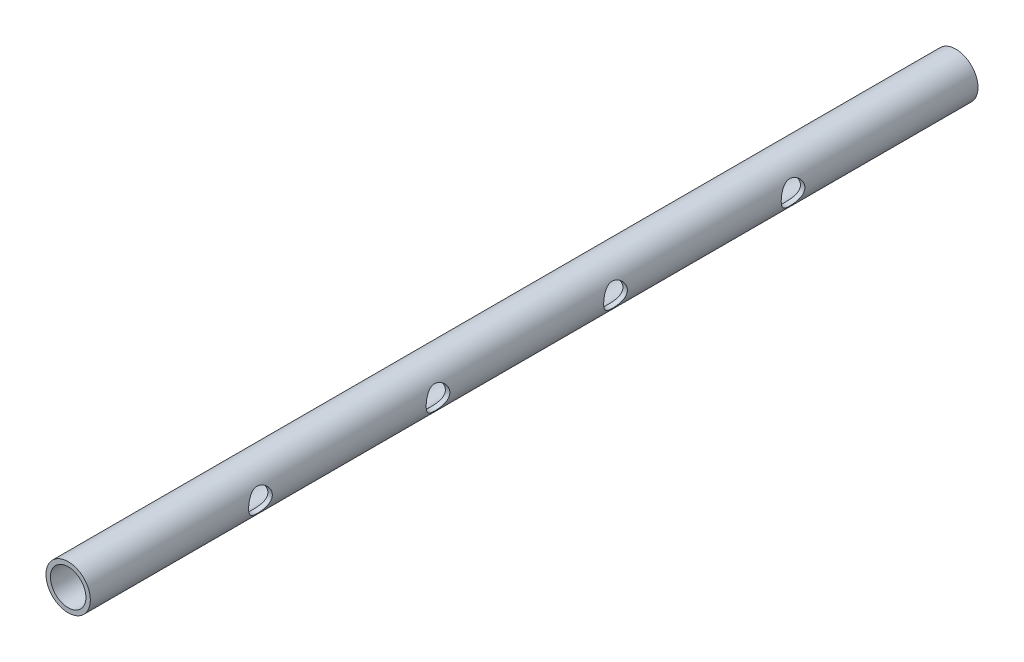
SolidWorks part; units mm, degrees
ref_plane "Front Plane" through (0, 0, 0) normal (0, 0, 1) x (1, 0, 0)
ref_plane "Top Plane" through (0, 0, 0) normal (0, 1, 0) x (1, 0, 0)
ref_plane "Right Plane" through (0, 0, 0) normal (1, 0, 0) x (0, 0, -1)
sketch "Sketch1" plane through (0, 0, 0) normal (0, 0, 1) x (1, 0, 0)
  circle A0 centre (0, 0) radius 7.5
  circle A1 centre (0, 0) radius 6
  dimension "D1" = 15
  dimension "D2" = 12
extrude "Boss-Extrude1" add sketch "Sketch1" along normal blind 300
ref_plane "Plane1" through (7.5, 0, 0) normal (1, 0, 0) x (0, 0, -1)
sketch "Sketch2" plane through (7.5, 0, 0) normal (1, 0, 0) x (0, 0, -1)
  line L0 (-297.5, -7.5) -> (-297.5, 7.5) construction
  circle A0 centre (-242.5, 0) radius 4
  circle A1 centre (-182.5, 0) radius 4
  circle A2 centre (-122.5, 0) radius 4
  circle A3 centre (-62.5, 0) radius 4
  dimension "D1" = 8
  dimension "D3" = 55
  dimension "D2" = 4
extrude "Cut-Extrude1" cut sketch "Sketch2" against normal blind 6
